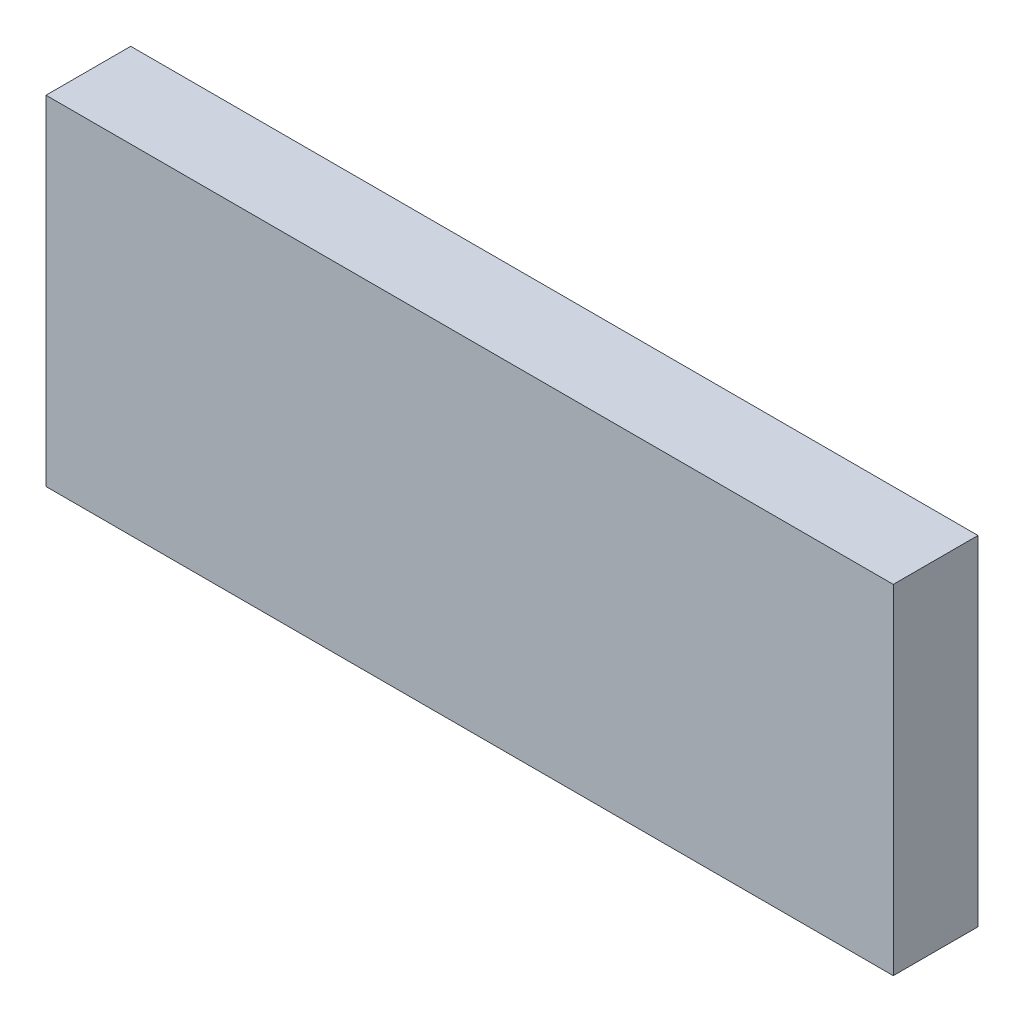
SolidWorks part; units mm, degrees
material "Silicon Rubber"
ref_plane "Front Plane" through (0, 0, 0) normal (0, 0, 1) x (1, 0, 0)
ref_plane "Top Plane" through (0, 0, 0) normal (0, 1, 0) x (1, 0, 0)
ref_plane "Right Plane" through (0, 0, 0) normal (1, 0, 0) x (0, 0, -1)
sketch "Sketch1" plane through (0, 0, 0) normal (0, 0, 1) x (1, 0, 0)
  line L1 (-50, 20) -> (50, 20)
  line L2 (-50, 20) -> (-50, -20)
  line L3 (-50, -20) -> (50, -20)
  line L4 (50, 20) -> (50, -20)
  line L5 (-50, 20) -> (50, -20) construction
  line L6 (-50, -20) -> (50, 20) construction
  point P0 (0, 0)
  dimension "D1" = 40
  dimension "D2" = 100
extrude "Boss-Extrude1" add sketch "Sketch1" along normal blind 10
